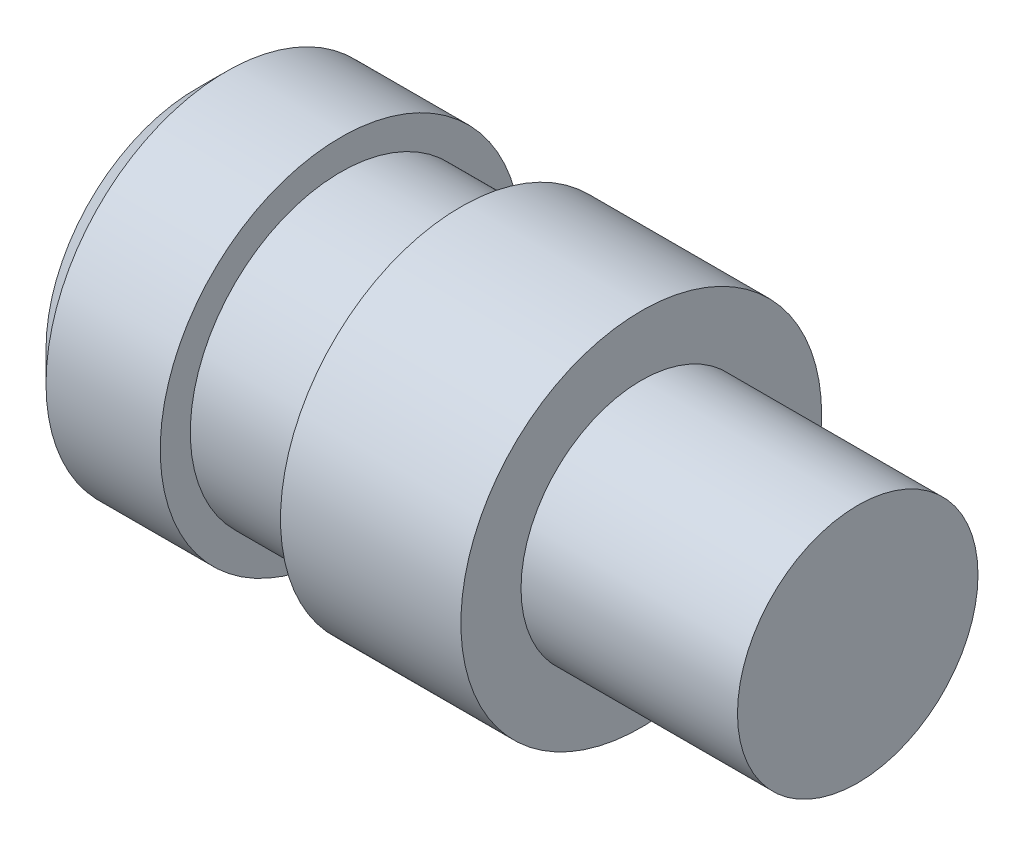
SolidWorks part; units mm, degrees
ref_plane "Face" through (0, 0, 0) normal (0, 0, 1) x (1, 0, 0)
ref_plane "Dessus" through (0, 0, 0) normal (0, 1, 0) x (1, 0, 0)
ref_plane "Droite" through (0, 0, 0) normal (1, 0, 0) x (0, 0, -1)
sketch "Esquisse1" plane through (0, 0, 0) normal (0, 0, 1) x (1, 0, 0)
  line L0 (0, 0) -> (0, 3)
  line L1 (0, 3) -> (2.4, 3)
  line L2 (2.4, 3) -> (2.4, 2.5)
  line L3 (2.4, 2.5) -> (4.4, 2.5)
  line L4 (4.4, 2.5) -> (4.4, 3)
  line L5 (4.4, 3) -> (7.4, 3)
  line L6 (7.4, 3) -> (7.4, 2)
  line L7 (7.4, 2) -> (11, 2)
  line L8 (11, 2) -> (11, 0)
  line L9 (11, 0) -> (0, 0)
  dimension "D1" = 3
  dimension "D2" = 3
  dimension "D3" = 2.5
  dimension "D4" = 2
  dimension "D5" = 2.4
  dimension "D6" = 2
  dimension "D7" = 3
  dimension "D8" = 11
  dimension "D9" = 3.6
revolve "Révolution1" add sketch "Esquisse1" angle 360 about L9
chamfer "Chanfrein1" distance 0.5 angle 45 1 edges at (0, 0, -3)
